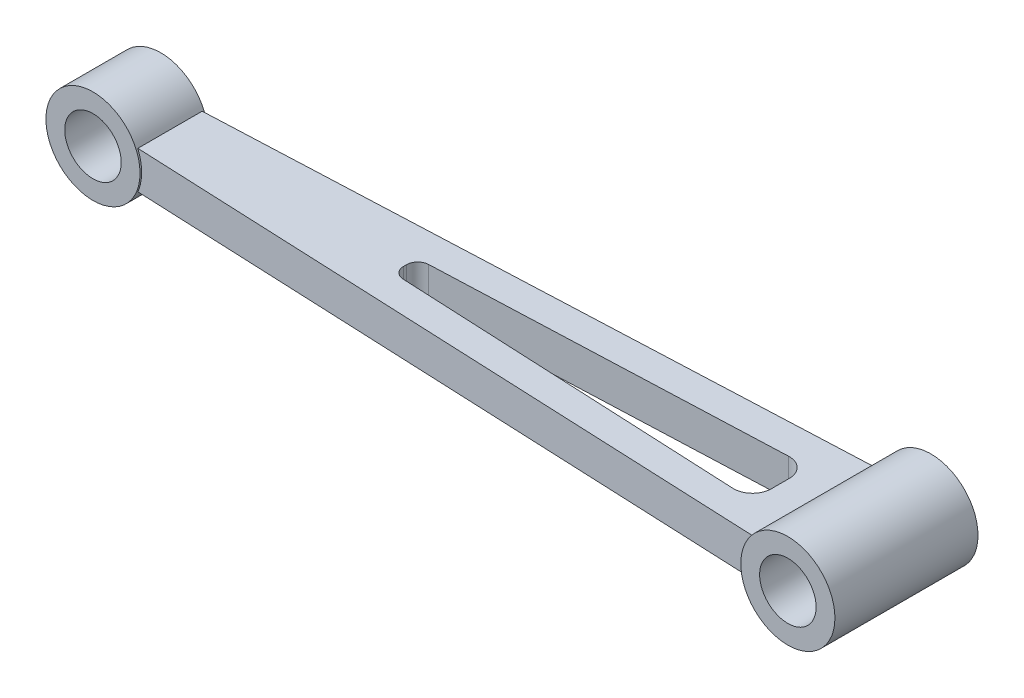
SolidWorks part; units mm, degrees
material "Ti-6Al-4VSolution treated and aged (SS)"
ref_plane "Front Plane" through (0, 0, 0) normal (0, 0, 1) x (1, 0, 0)
ref_plane "Top Plane" through (0, 0, 0) normal (0, 1, 0) x (1, 0, 0)
ref_plane "Right Plane" through (0, 0, 0) normal (1, 0, 0) x (0, 0, -1)
sketch "Sketch1" plane through (0, 0, 0) normal (0, 0, 1) x (1, 0, 0)
  circle A0 centre (0, 0) radius 7.5
  dimension "D1" = 15
extrude "Boss-Extrude1" add sketch "Sketch1" along normal mid plane 18
sketch "Sketch2" plane through (0, 0, 0) normal (0, 0, 1) x (1, 0, 0)
  line L0 (-83.2663, 0) -> (295.2271, 0) construction
  circle A0 centre (194.56, 0) radius 7.5
  dimension "D1" = 15
  dimension "D2" = 194.56
extrude "Boss-Extrude2" add sketch "Sketch2" along normal mid plane 38 separate body
sketch "Sketch3" plane through (0, 0, 0) normal (0, 1, 0) x (1, 0, 0)
  line L0 (0, 19.0952) -> (0, -33.7405) construction
  line L1 (7.5, 8.363) -> (187.06, 16.2)
  line L2 (7.5, -9) -> (7.5, 9) construction
  line L3 (187.06, 19) -> (187.06, -19) construction
  line L4 (187.06, 16.2) -> (187.06, -16.2048)
  line L5 (187.06, -16.2048) -> (7.5, -8.3623)
  line L6 (7.5, -8.3623) -> (7.5, 8.363)
  line L7 (-31.3303, 0) -> (230.7999, 0) construction
  point P9 (30, 9.345)
  point P12 (30, -9.345)
  dimension "D1" = 5
  dimension "D2" = 30
  dimension "D3" = 30
  dimension "D4" = 18.69
  dimension "D5" = 9.345
  dimension "D6" = 16.2
extrude "Boss-Extrude3" add sketch "Sketch3" along normal mid plane 10 separate body
sketch "Sketch4" plane through (0, 0, 0) normal (0, 0, 1) x (1, 0, 0)
  circle A0 centre (0, 0) radius 12.5
  dimension "D1" = 25
extrude "Boss-Extrude4" add sketch "Sketch4" along normal mid plane 18
sketch "Sketch6" plane through (0, 0, 0) normal (0, 0, 1) x (1, 0, 0)
  circle A0 centre (194.56, 0) radius 12.5
  dimension "D1" = 25
extrude "Boss-Extrude5" add sketch "Sketch6" along normal mid plane 38
sketch "Sketch7" plane through (0, 0, 0) normal (0, 0, 1) x (1, 0, 0)
  circle A0 centre (0, 0) radius 7.5
  circle A1 centre (194.56, 0) radius 7.5
  dimension "D1" = 15
  dimension "D2" = 15
extrude "Cut-Extrude1" cut sketch "Sketch7" against normal mid plane 38
sketch "Sketch8" plane through (0, 5, 0) normal (0, 1, 0) x (1, 0, 0)
  line L0 (-31.8393, 0.0628) -> (221.7757, -0.4378) construction
  line L1 (76.7694, 3.3689) -> (168.689, 7.0675)
  line L2 (173.89, 2.0715) -> (173.89, -2.7219)
  line L3 (168.6548, -7.7163) -> (76.7489, -3.3889)
  line L4 (73.89, -0.3923) -> (73.89, 0.3713)
  line L5 (11.4564, -8.5351) -> (183.1036, -16.032) construction
  line L6 (183.1036, 16.0273) -> (11.4564, 8.5357) construction
  line L8 (194.56, -19) -> (194.56, 19) construction
  arc A0 (173.89, -2.7219) -> (168.6548, -7.7163) centre (168.89, -2.7219) cw
  arc A1 (173.89, 2.0715) -> (168.689, 7.0675) centre (168.89, 2.0715) ccw
  arc A2 (73.89, -0.3923) -> (76.7489, -3.3889) centre (76.89, -0.3923) ccw
  arc A3 (73.89, 0.3713) -> (76.7694, 3.3689) centre (76.89, 0.3713) cw
  point P33 (173.89, -7.9628)
  point P36 (173.89, 7.2768)
  point P39 (73.89, -3.2543)
  point P42 (73.89, 3.253)
  dimension "D8" = 5
  dimension "D9" = 3
  dimension "D1" = 8.17
  dimension "D2" = 100
  dimension "D3" = 5
  dimension "D4" = 8
  dimension "D5" = 8
  dimension "D6" = 15.2396
  dimension "D7" = 7.62
extrude "Cut-Extrude2" cut sketch "Sketch8" against normal mid plane 38
